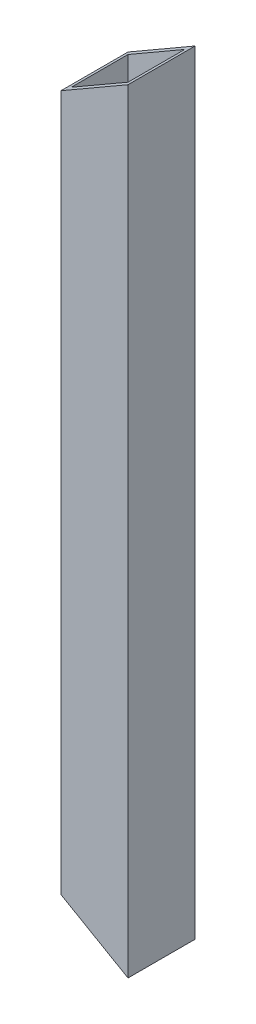
SolidWorks part; units mm, degrees
ref_plane "Front Plane" through (0, 0, 0) normal (0, 0, 1) x (1, 0, 0)
ref_plane "Top Plane" through (0, 0, 0) normal (0, 1, 0) x (1, 0, 0)
ref_plane "Right Plane" through (0, 0, 0) normal (1, 0, 0) x (0, 0, -1)
sketch "Sketch1" plane through (0, 0, 0) normal (0, 1, 0) x (1, 0, 0)
  line L0 (-6.5, 6.5) -> (6.5, 6.5)
  line L1 (-5.5, 5.5) -> (5.5, 5.5)
  line L2 (-5.5, 5.5) -> (-5.5, -5.5)
  line L3 (-5.5, -5.5) -> (5.5, -5.5)
  line L4 (5.5, 5.5) -> (5.5, -5.5)
  line L5 (-5.5, 5.5) -> (5.5, -5.5) construction
  line L6 (-5.5, -5.5) -> (5.5, 5.5) construction
  line L7 (6.5, 6.5) -> (6.5, -6.5)
  line L8 (-6.5, -6.5) -> (6.5, -6.5)
  line L9 (-6.5, 6.5) -> (-6.5, -6.5)
  point P1 (0, 0)
  dimension "D1" = 11
  dimension "D2" = 11
  dimension "D3" = 1
extrude "Boss-Extrude1" add sketch "Sketch1" along normal blind 150
sketch "Sketch2" plane through (0, 0, 6.5) normal (0, 0, 1) x (1, 0, 0)
  line L0 (6.5, 150) -> (-6.5, 142.4944)
  line L1 (-6.5, 150) -> (-6.5, 0) construction
extrude "Cut-Extrude1" cut sketch "Sketch2" against normal through all and the other way through all flip side to cut
sketch "Sketch3" plane through (0, 0, 6.5) normal (0, 0, 1) x (1, 0, 0)
  line L0 (6.5, 0) -> (-6.5, 7.5056)
  line L1 (-6.5, 142.4944) -> (-6.5, 0) construction
  line L6 (6.5, 0) -> (6.5, 150)
  line L7 (6.5, 150) -> (-6.5, 142.4944)
  line L8 (-6.5, 142.4944) -> (-6.5, 0)
  line L9 (-6.5, 0) -> (6.5, 0)
  line L10 (6.5, 0) -> (6.5, 150)
  line L11 (6.5, 150) -> (-6.5, 142.4944)
  line L12 (-6.5, 142.4944) -> (-6.5, 7.5056)
  dimension "D1" = 0
extrude "Cut-Extrude2" cut sketch "Sketch3" against normal through all both and the other way through all flip side to cut
